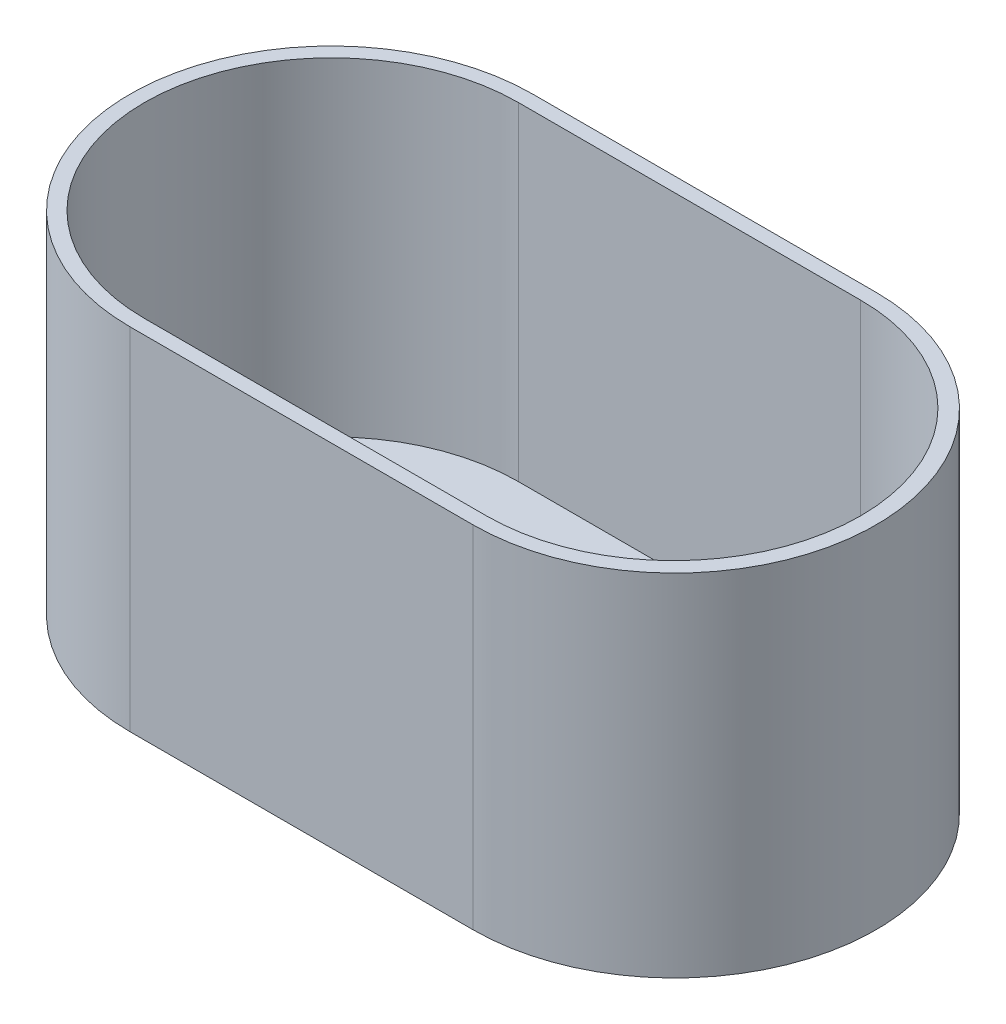
SolidWorks part; units mm, degrees
ref_plane "Front Plane" through (0, 0, 0) normal (0, 0, 1) x (1, 0, 0)
ref_plane "Top Plane" through (0, 0, 0) normal (0, 1, 0) x (1, 0, 0)
ref_plane "Right Plane" through (0, 0, 0) normal (1, 0, 0) x (0, 0, -1)
sketch "Sketch2" plane through (0, 0, 0) normal (0, 1, 0) x (1, 0, 0)
  line L0 (0, 0) -> (46, 0) construction
  line L1 (0, 27) -> (46, 27)
  line L2 (0, -27) -> (46, -27)
  arc A0 (0, 27) -> (0, -27) centre (0, 0) ccw
  arc A1 (46, -27) -> (46, 27) centre (46, 0) ccw
  point P3 (23, 0)
extrude "Boss-Extrude1" add sketch "Sketch2" along normal blind 44
sketch "Sketch3" plane through (0, 0, 0) normal (0, 1, 0) x (1, 0, 0)
  line L0 (0, 0) -> (45.8563, 0) construction
  line L1 (0, 25.0594) -> (45.8563, 25.0594)
  line L2 (0, -25.0594) -> (45.8563, -25.0594)
  arc A0 (0, 25.0594) -> (0, -25.0594) centre (0, 0) ccw
  arc A1 (45.8563, -25.0594) -> (45.8563, 25.0594) centre (45.8563, 0) ccw
  point P3 (22.9281, 0)
  point P8 (22.9281, 0)
extrude "Cut-Extrude1" cut sketch "Sketch3" along normal blind 46 and the other way blind 2
sketch "Sketch4" plane through (0, 0, 0) normal (0, 1, 0) x (1, 0, 0)
  line L0 (0, 0) -> (46, 0) construction
  line L1 (0, 27) -> (46, 27)
  line L2 (0, -27) -> (46, -27)
  arc A0 (0, 27) -> (0, -27) centre (0, 0) ccw
  arc A1 (46, -27) -> (46, 27) centre (46, 0) ccw
  point P3 (23, 0)
extrude "Boss-Extrude3" add sketch "Sketch4" against normal blind 3
sketch "Sketch5" plane through (0, 0, 0) normal (0, 1, 0) x (1, 0, 0)
  line L0 (-13.9397, 10.0856) -> (-13.9397, 4.6953)
  line L9 (-15.6758, 4.6953) -> (-15.6758, 11.7942)
  line L10 (-15.6758, 11.7942) -> (-9.2868, 11.7942)
  line L11 (-9.2868, 11.7942) -> (-9.2868, 10.0856)
  line L12 (-9.2868, 10.0856) -> (-13.9397, 10.0856)
  line L13 (-13.9397, 4.6953) -> (-15.6758, 4.6953)
  line L14 (26.3478, -10.1265) -> (26.3478, -4.7361)
  line L15 (28.0839, -4.7361) -> (28.0839, -11.8351)
  line L16 (28.0839, -11.8351) -> (21.6949, -11.8351)
  line L17 (21.6949, -11.8351) -> (21.6949, -10.1265)
  line L18 (21.6949, -10.1265) -> (26.3478, -10.1265)
  line L19 (26.3478, -4.7361) -> (28.0839, -4.7361)
extrude "Boss-Extrude4" add sketch "Sketch5" along normal blind 3
